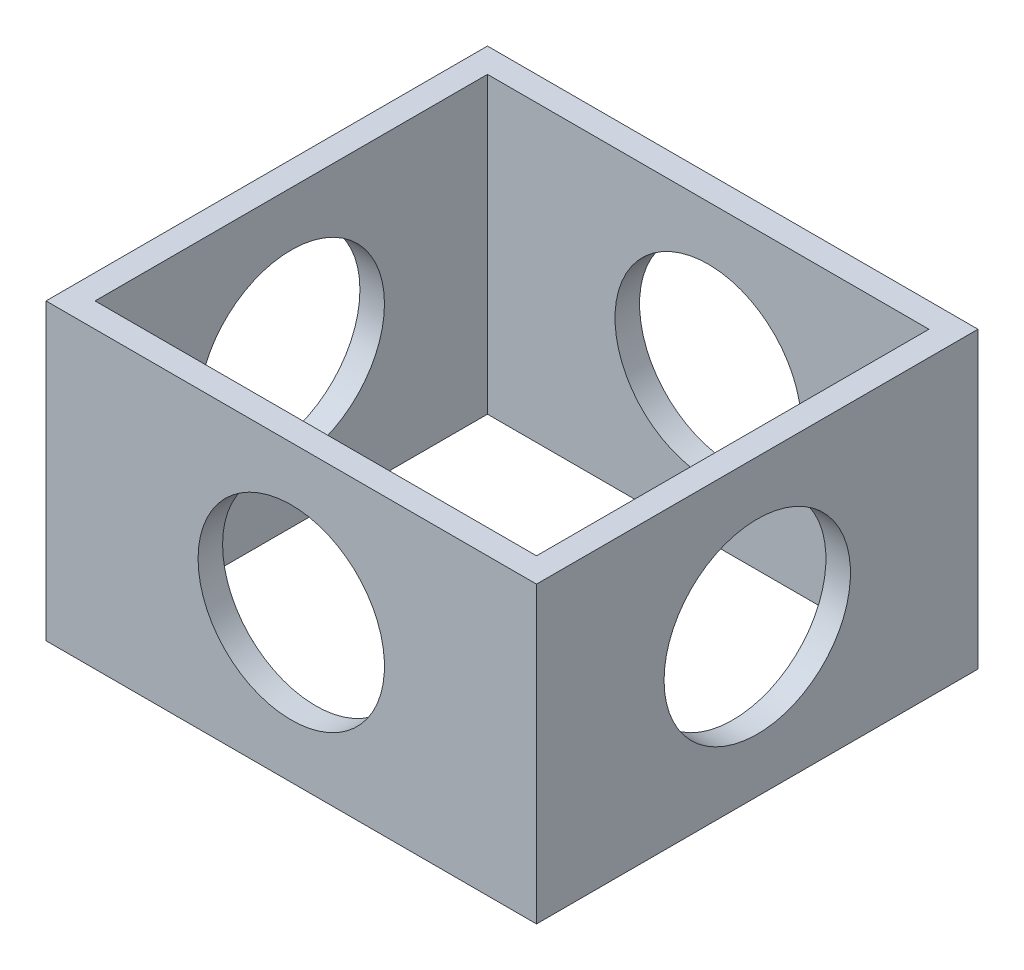
SolidWorks part; units mm, degrees
ref_plane "Front Plane" through (0, 0, 0) normal (0, 0, 1) x (1, 0, 0)
ref_plane "Top Plane" through (0, 0, 0) normal (0, 1, 0) x (1, 0, 0)
ref_plane "Right Plane" through (0, 0, 0) normal (1, 0, 0) x (0, 0, -1)
sketch "Sketch2" plane through (0, 0, 0) normal (0, 1, 0) x (1, 0, 0)
  line L1 (-25, -22.5) -> (25, -22.5)
  line L2 (-25, -22.5) -> (-25, 22.5)
  line L3 (-25, 22.5) -> (25, 22.5)
  line L4 (25, -22.5) -> (25, 22.5)
  line L5 (-25, -22.5) -> (25, 22.5) construction
  line L6 (-25, 22.5) -> (25, -22.5) construction
  line L7 (-22.5, -20) -> (22.5, -20)
  line L8 (-22.5, -20) -> (-22.5, 20)
  line L9 (-22.5, 20) -> (22.5, 20)
  line L10 (22.5, -20) -> (22.5, 20)
  line L11 (-22.5, -20) -> (22.5, 20) construction
  line L12 (-22.5, 20) -> (22.5, -20) construction
  point P0 (0, 0)
  point P6 (0, 0)
  dimension "D1" = 50
  dimension "D2" = 45
  dimension "D3" = 45
  dimension "D4" = 40
extrude "Boss-Extrude1" add sketch "Sketch2" along normal blind 30
sketch "Sketch3" plane through (0, 0, 0) normal (0, 1, 0) x (1, 0, 0)
  line L0 (0, 0) -> (0, 22.5) construction
  line L1 (25, 22.5) -> (-25, 22.5) construction
  line L2 (0, 22.5) -> (0, -22.5) construction
  line L3 (-25, -22.5) -> (25, -22.5) construction
  line L4 (-25, 0) -> (25, 0) construction
  line L5 (-25, 22.5) -> (-25, -22.5) construction
  line L6 (25, -22.5) -> (25, 22.5) construction
sketch "Sketch4" plane through (0, 0, 22.5) normal (0, 0, 1) x (1, 0, 0)
  line L0 (0, 0) -> (0, 30) construction
  line L1 (-25, 30) -> (25, 30) construction
  line L2 (0, 30) -> (25, 15) construction
  line L3 (25, 30) -> (25, 0) construction
  line L4 (25, 15) -> (-25, 15) construction
  line L5 (-25, 30) -> (-25, 0) construction
  circle A0 centre (0, 15) radius 9.5
  dimension "D1" = 19
extrude "Cut-Extrude1" cut sketch "Sketch4" against normal through all both and the other way through all
sketch "Sketch5" plane through (-25, 0, 0) normal (-1, 0, 0) x (0, 0, 1)
  line L0 (0, 0) -> (0, 30) construction
  line L1 (-22.5, 0) -> (22.5, 0) construction
  line L2 (-22.5, 30) -> (22.5, 30) construction
  line L3 (0, 30) -> (-22.5, 15) construction
  line L4 (-22.5, 30) -> (-22.5, 0) construction
  line L5 (-22.5, 15) -> (22.5, 15) construction
  line L6 (22.5, 30) -> (22.5, 0) construction
  circle A0 centre (0, 15) radius 9.5
  dimension "D1" = 19
extrude "Cut-Extrude2" cut sketch "Sketch5" against normal through all both and the other way through all
